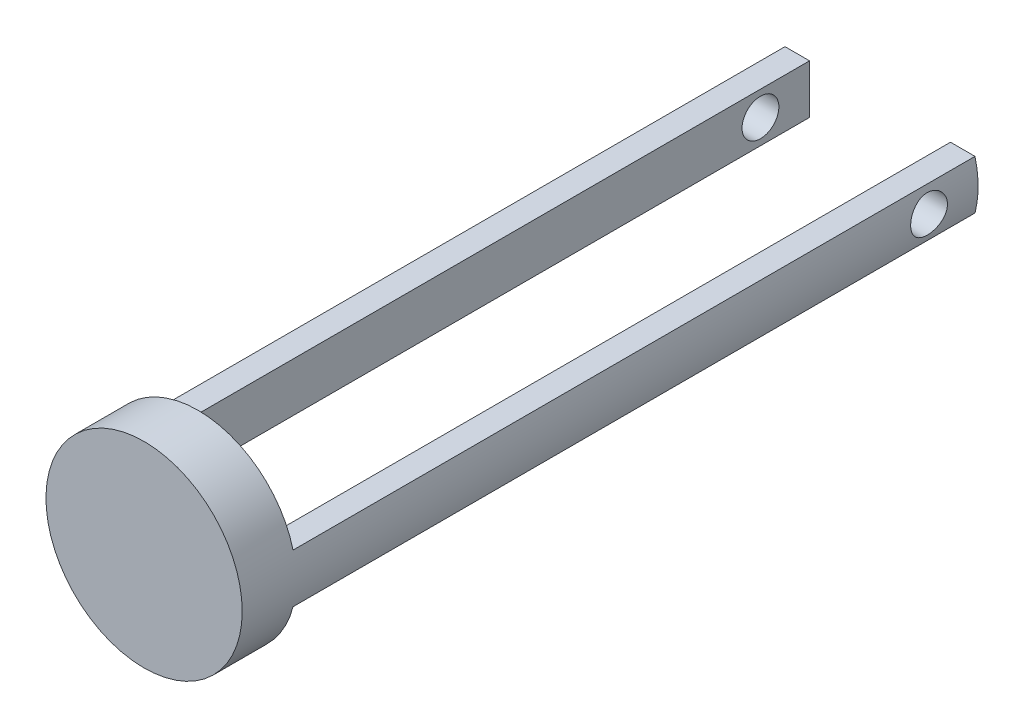
SolidWorks part; units mm, degrees
ref_plane "Front Plane" through (0, 0, 0) normal (0, 0, 1) x (1, 0, 0)
ref_plane "Top Plane" through (0, 0, 0) normal (0, 1, 0) x (1, 0, 0)
ref_plane "Right Plane" through (0, 0, 0) normal (1, 0, 0) x (0, 0, -1)
sketch "Sketch1" plane through (0, 0, 0) normal (0, 0, 1) x (1, 0, 0)
  circle A0 centre (0, 0) radius 50.8
  dimension "D1" = 101.6
extrude "Boss-Extrude1" add sketch "Sketch1" along normal blind 27.94
sketch "Sketch2" plane through (0, 0, 0) normal (0, 0, -1) x (-1, 0, 0)
  line L0 (-49.1869, 12.7) -> (-36.4869, 12.7)
  line L1 (-36.4869, 12.7) -> (-36.4869, -12.7)
  line L2 (-36.4869, -12.7) -> (-49.1869, -12.7)
  line L3 (49.1869, 12.7) -> (36.4869, 12.7)
  line L4 (36.4869, 12.7) -> (36.4869, -12.7)
  line L5 (36.4869, -12.7) -> (49.1869, -12.7)
  circle A0 centre (0, 0) radius 50.8 construction
  arc A1 (-49.1869, 12.7) -> (-49.1869, -12.7) centre (0, 0) ccw
  arc A2 (49.1869, 12.7) -> (49.1869, -12.7) centre (0, 0) cw
  point P12 (-36.4869, 0)
  point P13 (36.4869, 0)
  dimension "D1" = 25.4
  dimension "D2" = 12.7
extrude "Boss-Extrude2" add sketch "Sketch2" along normal blind 353.06
sketch "Sketch3" plane through (0, 0, 0) normal (1, 0, 0) x (0, 0, -1)
  line L0 (-27.94, 50.8) -> (-27.94, -50.8) construction
  circle A0 centre (327.66, 0) radius 9.525
  dimension "D1" = 19.05
  dimension "D2" = 355.6
extrude "Cut-Extrude1" cut sketch "Sketch3" against normal through all both and the other way through all
equation "\"B\"= 13.9"
equation "\"A\"= 169"
equation "\"C\"= 2.7"
